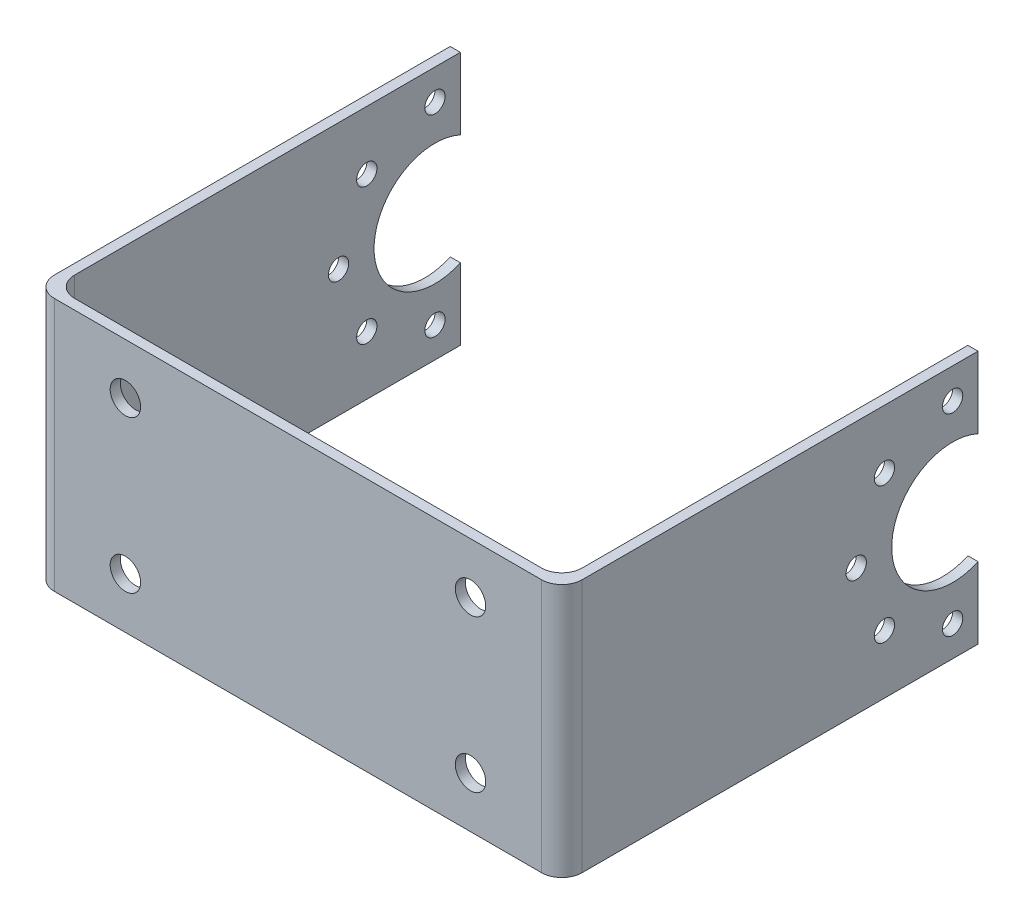
SolidWorks part; units mm, degrees
material "1060 Alloy"
ref_plane "Front Plane" through (0, 0, 0) normal (0, 0, 1) x (1, 0, 0)
ref_plane "Top Plane" through (0, 0, 0) normal (0, 1, 0) x (1, 0, 0)
ref_plane "Right Plane" through (0, 0, 0) normal (1, 0, 0) x (0, 0, -1)
sketch "Sketch1" plane through (0, 0, 0) normal (0, 1, 0) x (1, 0, 0)
  line L1 (-21.5, 0.5) -> (28.5, 0.5)
  line L2 (-22.5, 0.5) -> (-22.5, -0.5)
  line L3 (-22.5, -0.5) -> (29.5, -0.5)
  line L4 (29.5, 0.5) -> (29.5, -0.5)
  line L8 (29.5, 0.5) -> (29.5, 40.5)
  line L9 (29.5, 40.5) -> (28.5, 40.5)
  line L10 (28.5, 0.5) -> (28.5, 40.5)
  line L12 (-22.5, 0.5) -> (-22.5, 40.5)
  line L13 (-22.5, 40.5) -> (-21.5, 40.5)
  line L14 (-21.5, 0.5) -> (-21.5, 40.5)
  point P0 (0, 0)
  dimension "D1" = 52
  dimension "D2" = 1
  dimension "D3" = 1
  dimension "D4" = 1
  dimension "D5" = 40
  dimension "D6" = 40
extrude "Boss-Extrude1" add sketch "Sketch1" along normal blind 25
sketch "Sketch2" plane through (29.5, 0, 0) normal (1, 0, 0) x (0, 0, -1)
  line L1 (40.5, 12.5) -> (38, 12.5)
  line L2 (40.5, 25) -> (40.5, 0) construction
  line L3 (32, 12.5) -> (28.5, 12.5)
  circle A0 centre (38, 12.5) radius 6
  circle A1 centre (28.5, 12.5) radius 1
  circle A2 centre (31.2825, 19.2175) radius 1
  circle A3 centre (38, 22) radius 1
  circle A4 centre (44.7175, 19.2175) radius 1
  circle A5 centre (47.5, 12.5) radius 1
  circle A6 centre (44.7175, 5.7825) radius 1
  circle A7 centre (38, 3) radius 1
  circle A8 centre (31.2825, 5.7825) radius 1
  point P25 (38, 12.5)
  dimension "D1" = 2.5
  dimension "D3" = 3.5
  dimension "D2" = 12
  dimension "D4" = 2
  dimension "D5" = 8
extrude "Cut-Extrude1" cut sketch "Sketch2" against normal through all
fillet "Fillet2" radius 2 4 edges at (-22.5, 12.5, 0.5) (-21.5, 12.5, -0.5) (29.5, 12.5, 0.5) (28.5, 12.5, -0.5)
sketch "Sketch3" plane through (0, 0, 0.5) normal (0, 0, 1) x (1, 0, 0)
  line L0 (3.5, 25) -> (3.5, 20)
  line L2 (3.5, 20) -> (-13.5, 20)
  line L3 (3.5, 20) -> (20.5, 20)
  line L4 (-20.5, 25) -> (27.5, 25) construction
  line L5 (3.5, 0) -> (3.5, 5)
  line L6 (-20.5, 0) -> (27.5, 0) construction
  line L8 (3.5, 5) -> (-13.5, 5)
  line L9 (3.5, 5) -> (20.5, 5)
  circle A0 centre (-13.5, 20) radius 1.5
  circle A1 centre (20.5, 20) radius 1.5
  circle A2 centre (-13.5, 5) radius 1.5
  circle A3 centre (20.5, 5) radius 1.5
  dimension "D3" = 3
  dimension "D4" = 3
  dimension "D9" = 3
  dimension "D10" = 3
  dimension "D1" = 17
  dimension "D2" = 17
  dimension "D5" = 5
  dimension "D6" = 5
  dimension "D7" = 17
  dimension "D8" = 17
extrude "Cut-Extrude2" cut sketch "Sketch3" against normal through all
